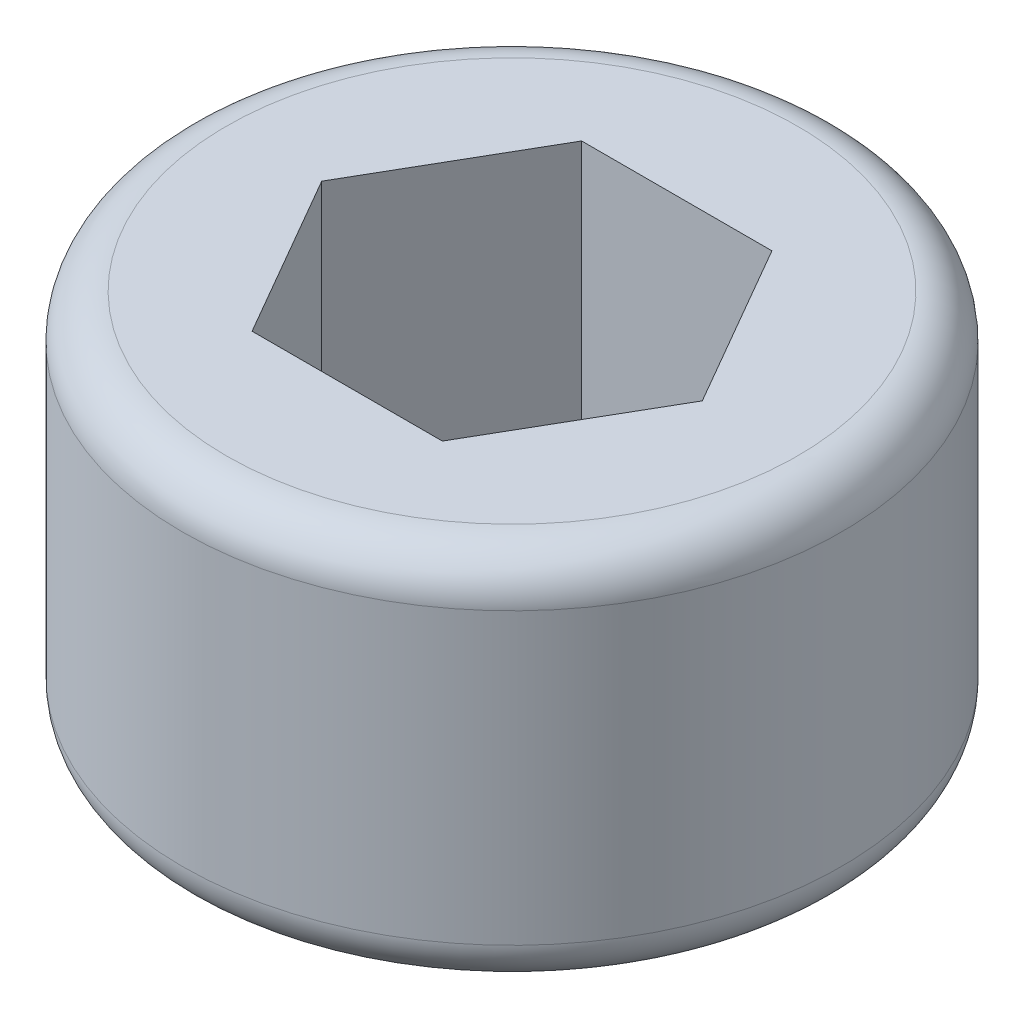
SolidWorks part; units mm, degrees
material "AISI 304"
ref_plane "前视基准面" through (0, 0, 0) normal (0, 0, 1) x (1, 0, 0)
ref_plane "上视基准面" through (0, 0, 0) normal (0, 1, 0) x (1, 0, 0)
ref_plane "右视基准面" through (0, 0, 0) normal (1, 0, 0) x (0, 0, -1)
sketch "草图1" plane through (0, 0, 0) normal (0, 1, 0) x (1, 0, 0)
  circle A0 centre (0, 0) radius 1.5
  dimension "D1" = 3
extrude "螺纹长度" add sketch "草图1" along normal blind 2
sketch "草图2" plane through (0, 2, 0) normal (0, 1, 0) x (1, 0, 0)
  line L1 (0.866, 0) -> (0.433, 0.75)
  line L2 (0.433, 0.75) -> (-0.433, 0.75)
  line L3 (-0.433, 0.75) -> (-0.866, 0)
  line L4 (-0.866, 0) -> (-0.433, -0.75)
  line L5 (-0.433, -0.75) -> (0.433, -0.75)
  line L6 (0.433, -0.75) -> (0.866, 0)
  circle A0 centre (0, 0) radius 0.75 construction
  dimension "D1" = 1.5
extrude "内六角深度" cut sketch "草图2" against normal blind 1.2
ref_axis "基准轴1" through (0, 2, 0) along (0, -1, 0)
sketch "草图3" plane through (0, 0, 0) normal (0, 0, 1) x (1, 0, 0)
  line L0 (0, -0.5) -> (0.866, 0) construction
  line L1 (1.5, 0) -> (1.5, 2) construction
  line L2 (1.5, 0.366) -> (1.5, 0)
  line L3 (1.5, -0.5) -> (0, -0.5) construction
  line L4 (0, 2) -> (0, 0) construction
  line L5 (-1.5, 0) -> (1.5, 0) construction
  line L6 (0.866, 0) -> (1.5, 0)
  line L7 (1.5, 0) -> (1.5, -0.5) construction
  line L8 (0.866, 0) -> (1.5, 0.366)
  dimension "D1" = 60
  dimension "D2" = 0.5
revolve "切除-旋转4" cut sketch "草图3" angle 360 about axis through (0, 2, 0) along (0, -1, 0)
fillet "圆角1" radius 0.2 2 edges at (0, 2, 1.5) (0, 0.366, 1.5)
